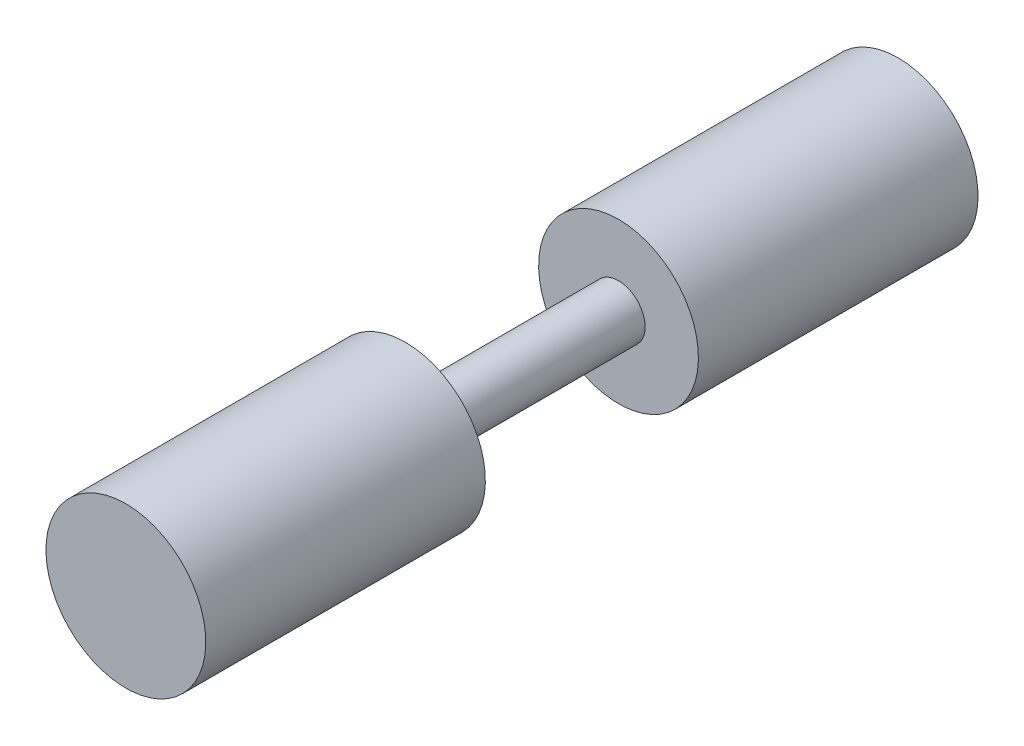
SolidWorks part; units mm, degrees
material "6061 Alloy"
ref_plane "Front Plane" through (0, 0, 0) normal (0, 0, 1) x (1, 0, 0)
ref_plane "Top Plane" through (0, 0, 0) normal (0, 1, 0) x (1, 0, 0)
ref_plane "Right Plane" through (0, 0, 0) normal (1, 0, 0) x (0, 0, -1)
sketch "Sketch1" plane through (0, 0, 0) normal (1, 0, 0) x (0, 0, -1)
  line L0 (92.075, 0) -> (-92.075, 0)
  line L1 (-92.075, 0) -> (-92.075, 19.05)
  line L2 (-92.075, 19.05) -> (-25.4, 19.05)
  line L3 (-25.4, 19.05) -> (-25.4, 6.35)
  line L4 (-25.4, 6.35) -> (25.4, 6.35)
  line L5 (25.4, 6.35) -> (25.4, 19.05)
  line L6 (25.4, 19.05) -> (92.075, 19.05)
  line L7 (92.075, 19.05) -> (92.075, 0)
  point P4 (0, 0)
  dimension "D1" = 66.675
  dimension "D2" = 19.05
  dimension "D3" = 6.35
  dimension "D4" = 184.15
  dimension "D5" = 50.8
revolve "Revolve1" add sketch "Sketch1" angle 360 about L0
